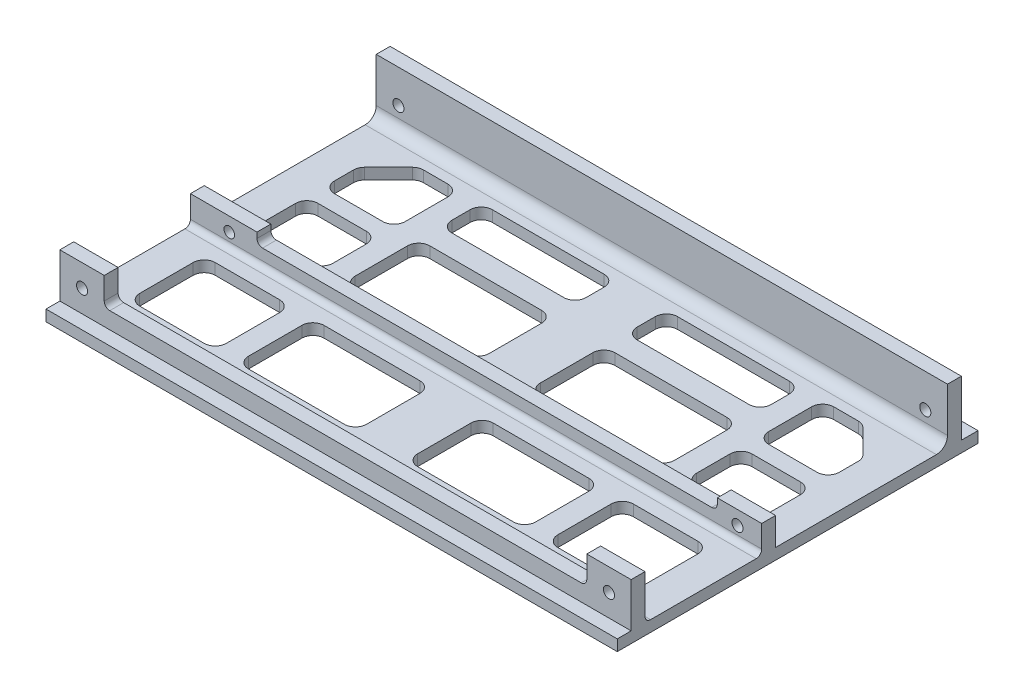
SolidWorks part; units mm, degrees
ref_plane "Front Plane" through (0, 0, 0) normal (0, 0, 1) x (1, 0, 0)
ref_plane "Top Plane" through (0, 0, 0) normal (0, 1, 0) x (1, 0, 0)
ref_plane "Right Plane" through (0, 0, 0) normal (1, 0, 0) x (0, 0, -1)
sketch "Sketch1" plane through (0, 0, 0) normal (0, 1, 0) x (1, 0, 0)
  line L1 (-51.5, -31.02) -> (51.5, -31.02)
  line L2 (-51.5, -31.02) -> (-51.5, 31.02)
  line L3 (-51.5, 31.02) -> (51.5, 31.02)
  line L4 (51.5, -31.02) -> (51.5, 31.02)
  line L5 (-51.5, -31.02) -> (51.5, 31.02) construction
  line L6 (-51.5, 31.02) -> (51.5, -31.02) construction
  point P0 (0, 0)
  dimension "D1" = 62.04
  dimension "D2" = 103
extrude "Boss-Extrude1" add sketch "Sketch1" along normal blind 2
sketch "Sketch2" plane through (0, 0, -31.02) normal (0, 0, -1) x (-1, 0, 0)
  line L4 (-51.5, 0) -> (51.5, 0)
  line L5 (51.5, 0) -> (51.5, 2)
  line L6 (51.5, 2) -> (-51.5, 2)
  line L7 (-51.5, 2) -> (-51.5, 0)
  line L8 (-51.5, 0) -> (51.5, 0)
  line L9 (51.5, 0) -> (51.5, 2)
  line L10 (51.5, 2) -> (-51.5, 2)
  line L11 (-51.5, 2) -> (-51.5, 0)
  dimension "D1" = 0
extrude "Boss-Extrude2" add sketch "Sketch2" along normal blind 3
sketch "Sketch5" plane through (0, 2, 0) normal (0, 1, 0) x (1, 0, 0)
  line L0 (51.5, 31.02) -> (43.5, 31.02)
  line L1 (51.5, -31.02) -> (51.5, 34.02) construction
  line L2 (43.5, 31.02) -> (43.5, 28.52)
  line L3 (43.5, 28.52) -> (51.5, 28.52)
  line L4 (51.5, 28.52) -> (51.5, 31.02)
  line L5 (0, -38.0579) -> (0, 51.3631) construction
  line L6 (-51.5, 34.02) -> (51.5, 34.02) construction
  dimension "D1" = 3
  dimension "D2" = 2.5
  dimension "D3" = 8
extrude "Boss-Extrude4" add sketch "Sketch5" along normal blind 10
sketch "Sketch6" plane through (0, 2, 0) normal (0, 1, 0) x (1, 0, 0)
  line L0 (43.5, 28.52) -> (0, 28.52)
  line L1 (0, 30.9258) -> (43.5, 31.02)
  line L2 (43.5, 31.02) -> (43.5, 28.52)
  line L3 (0, 28.52) -> (0, 30.9258)
extrude "Boss-Extrude5" add sketch "Sketch6" along normal blind 10
ref_plane "Plane1" through (0, 0, 0) normal (1, 0, 0) x (0, 0, -1)
sketch "Sketch7" plane through (0, 0, -28.52) normal (0, 0, 1) x (1, 0, 0)
  line L0 (0, 2) -> (51.5, 2) construction
  line L1 (51.5, 12) -> (51.5, 2) construction
  circle A0 centre (47.5, 6) radius 1
  dimension "D1" = 2
  dimension "D2" = 4
  dimension "D3" = 4
extrude "Cut-Extrude1" cut sketch "Sketch7" against normal blind 3
mirror "Mirror1" about plane through (0, 0, 0) normal (1, 0, 0) of "Boss-Extrude5", "Cut-Extrude1", "Boss-Extrude4"
fillet "Fillet2" radius 2 1 edges at (0, 2, -28.52)
sketch "Sketch8" plane through (0, 2, 0) normal (0, 1, 0) x (1, 0, 0)
  line L0 (51.5, -4.98) -> (-51.5, -4.98)
  line L3 (-51.5, -4.98) -> (-51.5, -2.48)
  line L4 (-51.5, -2.48) -> (51.5, -2.48)
  line L5 (51.5, -2.48) -> (51.5, -4.98)
  line L10 (-51.5, -31.02) -> (51.5, -31.02) construction
  dimension "D1" = 2.5
  dimension "D2" = 2.5
  dimension "D3" = 26.04
extrude "Boss-Extrude6" add sketch "Sketch8" along normal blind 3
sketch "Sketch9" plane through (0, 5, 0) normal (0, 1, 0) x (1, 0, 0)
  line L0 (51.5, -4.98) -> (43.5, -4.98)
  line L1 (-51.5, -4.98) -> (51.5, -4.98) construction
  line L2 (43.5, -4.98) -> (43.5, -2.48)
  line L3 (51.5, -2.48) -> (-51.5, -2.48) construction
  line L4 (43.5, -2.48) -> (51.5, -2.48)
  line L5 (51.5, -2.48) -> (51.5, -4.98)
  dimension "D1" = 8
extrude "Boss-Extrude7" add sketch "Sketch9" along normal blind 2
sketch "Sketch11" plane through (0, 0, 4.98) normal (0, 0, 1) x (1, 0, 0)
  line L1 (51.5, 7) -> (51.5, 2) construction
  circle A0 centre (47.13, 4.5) radius 1
  dimension "D1" = 2
  dimension "D2" = 4.37
extrude "Cut-Extrude3" cut sketch "Sketch11" against normal blind 22
fillet "Fillet4" radius 1 1 edges at (0, 2, 4.98)
sketch "Sketch12" plane through (0, 5, 0) normal (0, 1, 0) x (1, 0, 0)
  line L0 (-51.5, -4.98) -> (-39.5, -4.98)
  line L1 (-51.5, -4.98) -> (43.5, -4.98) construction
  line L2 (-39.5, -4.98) -> (-39.5, -2.48)
  line L3 (43.5, -2.48) -> (-51.5, -2.48) construction
  line L4 (-39.5, -2.48) -> (-51.5, -2.48)
  line L5 (-51.5, -2.48) -> (-51.5, -4.98)
  dimension "D1" = 12
extrude "Boss-Extrude8" add sketch "Sketch12" along normal blind 2
fillet "Fillet5" radius 1 1 edges at (-39.5, 5, 3.73)
sketch "Sketch13" plane through (0, 0, 4.98) normal (0, 0, 1) x (1, 0, 0)
  line L0 (-51.5, 7) -> (-51.5, 3) construction
  line L1 (-51.5, 7) -> (-39.5, 7) construction
  circle A0 centre (-44.5, 4.5) radius 0.9513
  dimension "D1" = 7
  dimension "D2" = 2.5
extrude "Cut-Extrude4" cut sketch "Sketch13" against normal blind 12
fillet "Fillet6" radius 1 1 edges at (43.5, 5, 3.73)
sketch "Sketch14" plane through (0, 2, 0) normal (0, 1, 0) x (1, 0, 0)
  line L0 (51.5, -28.52) -> (-51.5, -28.52)
  line L1 (-51.5, -28.52) -> (-51.5, -26.02)
  line L2 (-51.5, -5.98) -> (-51.5, -31.02) construction
  line L3 (-51.5, -26.02) -> (51.5, -26.02)
  line L4 (51.5, -31.02) -> (51.5, -5.98) construction
  line L5 (51.5, -26.02) -> (51.5, -28.52)
  line L6 (-51.5, -31.02) -> (51.5, -31.02) construction
  dimension "D1" = 2.5
  dimension "D2" = 2.5
extrude "Boss-Extrude9" add sketch "Sketch14" along normal blind 3
sketch "Sketch15" plane through (0, 5, 0) normal (0, 1, 0) x (1, 0, 0)
  line L0 (51.5, -28.52) -> (43.5, -28.52)
  line L1 (-51.5, -28.52) -> (51.5, -28.52) construction
  line L2 (43.5, -28.52) -> (43.5, -26.02)
  line L3 (51.5, -26.02) -> (-51.5, -26.02) construction
  line L4 (43.5, -26.02) -> (51.5, -26.02)
  line L5 (51.5, -26.02) -> (51.5, -28.52)
  line L6 (-51.5, -28.52) -> (-51.5, -26.02)
  line L7 (-51.5, -26.02) -> (-43.5, -26.02)
  line L8 (-43.5, -26.02) -> (-43.5, -28.52)
  line L9 (-43.5, -28.52) -> (-51.5, -28.52)
  dimension "D1" = 8
  dimension "D2" = 8
  dimension "D3" = 2.5
extrude "Boss-Extrude10" add sketch "Sketch15" along normal blind 5
sketch "Sketch16" plane through (0, 0, 31.02) normal (0, 0, 1) x (1, 0, 0)
  line L0 (43.5, 10) -> (51.5, 10) construction
  line L2 (51.5, 2) -> (51.5, 0) construction
  line L3 (-51.5, 2) -> (-51.5, 0) construction
  line L4 (-51.5, 10) -> (-43.5, 10) construction
  circle A0 centre (47.5, 6) radius 1
  circle A1 centre (-47.5, 6) radius 1
  dimension "D5" = 2
  dimension "D6" = 2
  dimension "D1" = 4
  dimension "D2" = 4
  dimension "D3" = 4
  dimension "D4" = 4
extrude "Cut-Extrude5" cut sketch "Sketch16" against normal blind 15
fillet "Fillet7" radius 1 3 edges at (0, 2, 26.02) (43.5, 5, 27.27) (-43.5, 5, 27.27)
sketch "Sketch17" plane through (0, 2, 0) normal (0, 1, 0) x (1, 0, 0)
  line L0 (43.5, -22.1211) -> (31.8853, -22.1211)
  line L1 (29.8853, -20.1211) -> (29.8853, -10.5043)
  line L2 (31.8853, -8.5043) -> (43.5, -8.5043)
  line L3 (45.5, -10.5043) -> (45.5, -20.1211)
  line L4 (25.8853, -20.1211) -> (25.8853, -10.5043)
  line L5 (23.8853, -8.5043) -> (6.6087, -8.5043)
  line L6 (4.6087, -10.5043) -> (4.6087, -20.1211)
  line L7 (6.6087, -22.1211) -> (23.8853, -22.1211)
  line L8 (44.9142, 19.849) -> (40.6192, 24.144)
  line L9 (39.205, 24.7298) -> (34.7808, 24.7298)
  line L10 (32.7808, 22.7298) -> (32.7808, 15.003)
  line L11 (34.7808, 13.003) -> (43.5, 13.003)
  line L12 (45.5, 15.003) -> (45.5, 18.4348)
  line L13 (43.5, 10.003) -> (34.7808, 10.003)
  line L14 (32.7808, 8.003) -> (32.7808, 2)
  line L15 (34.7808, 0) -> (43.5, 0)
  line L16 (45.5, 2) -> (45.5, 8.003)
  line L17 (28.7808, 2) -> (28.7808, 11.4521)
  line L18 (26.7808, 13.4521) -> (6.6087, 13.4521)
  line L19 (4.6087, 11.4521) -> (4.6087, 2)
  line L20 (6.6087, 0) -> (26.7808, 0)
  line L21 (28.7808, 19.4521) -> (28.7808, 22.7298)
  line L22 (26.7808, 24.7298) -> (6.6087, 24.7298)
  line L23 (4.6087, 22.7298) -> (4.6087, 19.4521)
  line L24 (6.6087, 17.4521) -> (26.7808, 17.4521)
  line L25 (51.5, -25.02) -> (51.5, -5.98) construction
  line L26 (51.5, -2.48) -> (51.5, 26.52) construction
  arc A0 (4.6087, 2) -> (6.6087, 0) centre (6.6087, 2) ccw
  arc A1 (28.7808, 2) -> (26.7808, 0) centre (26.7808, 2) cw
  arc A2 (28.7808, 11.4521) -> (26.7808, 13.4521) centre (26.7808, 11.4521) ccw
  arc A3 (6.6087, 13.4521) -> (4.6087, 11.4521) centre (6.6087, 11.4521) ccw
  arc A4 (4.6087, 19.4521) -> (6.6087, 17.4521) centre (6.6087, 19.4521) ccw
  arc A5 (6.6087, 24.7298) -> (4.6087, 22.7298) centre (6.6087, 22.7298) ccw
  arc A6 (28.7808, 22.7298) -> (26.7808, 24.7298) centre (26.7808, 22.7298) ccw
  arc A7 (28.7808, 19.4521) -> (26.7808, 17.4521) centre (26.7808, 19.4521) cw
  arc A8 (32.7808, 15.003) -> (34.7808, 13.003) centre (34.7808, 15.003) ccw
  arc A9 (34.7808, 24.7298) -> (32.7808, 22.7298) centre (34.7808, 22.7298) ccw
  arc A10 (40.6192, 24.144) -> (39.205, 24.7298) centre (39.205, 22.7298) ccw
  arc A11 (44.9142, 19.849) -> (45.5, 18.4348) centre (43.5, 18.4348) cw
  arc A12 (43.5, 13.003) -> (45.5, 15.003) centre (43.5, 15.003) ccw
  arc A13 (32.7808, 2) -> (34.7808, 0) centre (34.7808, 2) ccw
  arc A14 (34.7808, 10.003) -> (32.7808, 8.003) centre (34.7808, 8.003) ccw
  arc A15 (43.5, 10.003) -> (45.5, 8.003) centre (43.5, 8.003) cw
  arc A16 (43.5, 0) -> (45.5, 2) centre (43.5, 2) ccw
  arc A17 (4.6087, -20.1211) -> (6.6087, -22.1211) centre (6.6087, -20.1211) ccw
  arc A18 (6.6087, -8.5043) -> (4.6087, -10.5043) centre (6.6087, -10.5043) ccw
  arc A19 (25.8853, -10.5043) -> (23.8853, -8.5043) centre (23.8853, -10.5043) ccw
  arc A20 (25.8853, -20.1211) -> (23.8853, -22.1211) centre (23.8853, -20.1211) cw
  arc A21 (31.8853, -22.1211) -> (29.8853, -20.1211) centre (31.8853, -20.1211) cw
  arc A22 (29.8853, -10.5043) -> (31.8853, -8.5043) centre (31.8853, -10.5043) cw
  arc A23 (43.5, -8.5043) -> (45.5, -10.5043) centre (43.5, -10.5043) cw
  arc A24 (43.5, -22.1211) -> (45.5, -20.1211) centre (43.5, -20.1211) ccw
  point P30 (29.8853, -15.3127)
  point P37 (28.7808, 13.4521)
  point P40 (4.6087, 13.4521)
  point P71 (4.6087, -8.5043)
  dimension "D9" = 2
  dimension "D1" = 6
  dimension "D2" = 6
  dimension "D3" = 6
  dimension "D4" = 4
  dimension "D5" = 4
  dimension "D6" = 4
  dimension "D7" = 4
  dimension "D8" = 3
extrude "Cut-Extrude6" cut sketch "Sketch17" against normal blind 5
mirror "Mirror4" about plane through (0, 0, 0) normal (1, 0, 0) of "Cut-Extrude6"
